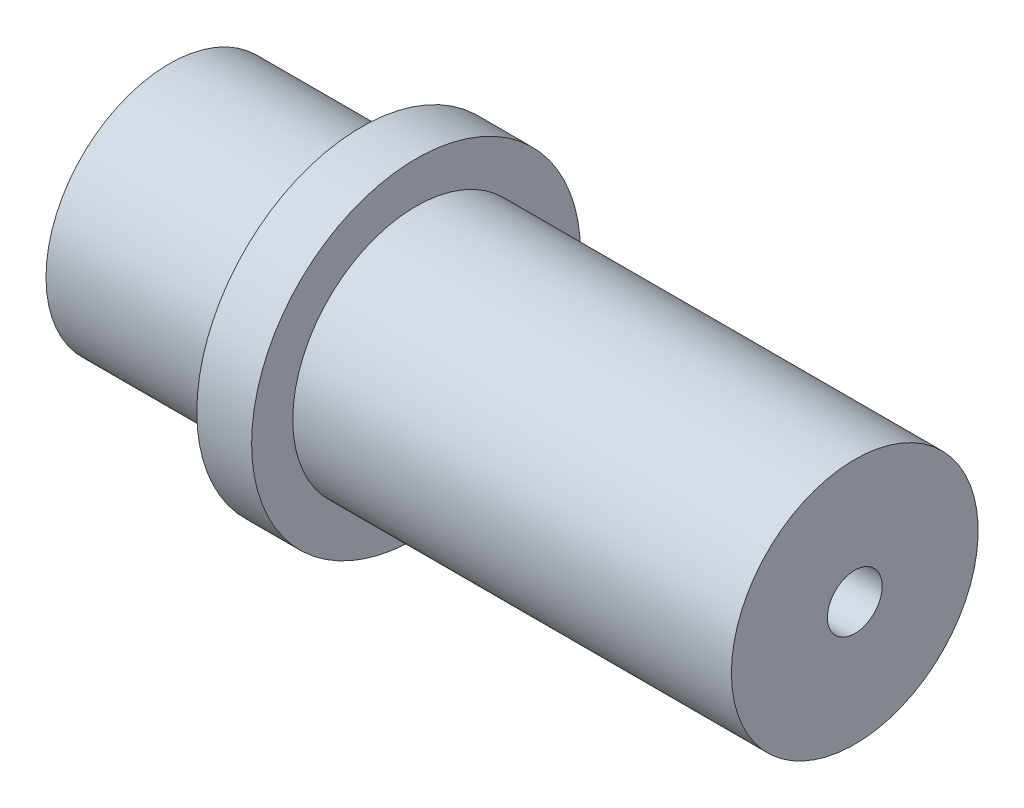
SolidWorks part; units mm, degrees
ref_plane "Front Plane" through (0, 0, 0) normal (0, 0, 1) x (1, 0, 0)
ref_plane "Top Plane" through (0, 0, 0) normal (0, 1, 0) x (1, 0, 0)
ref_plane "Right Plane" through (0, 0, 0) normal (1, 0, 0) x (0, 0, -1)
sketch "Sketch1" plane through (0, 0, 0) normal (0, 0, 1) x (1, 0, 0)
  line L0 (0, 0) -> (95.0095, 0) construction
  line L1 (0, 1.875) -> (0, 5.625)
  line L2 (0, 5.625) -> (8.75, 5.625)
  line L3 (8.75, 5.625) -> (8.75, 7.5)
  line L4 (8.75, 7.5) -> (11.25, 7.5)
  line L5 (11.25, 7.5) -> (11.25, 5.625)
  line L6 (11.25, 5.625) -> (31.25, 5.625)
  line L7 (31.25, 5.625) -> (31.25, 1.25)
  line L8 (31.25, 1.25) -> (21.75, 1.25)
  line L9 (21.75, 1.25) -> (21.75, 1.875)
  line L10 (21.75, 1.875) -> (0, 1.875)
  dimension "D1" = 31.25
  dimension "D2" = 2.5
  dimension "D3" = 20
  dimension "D4" = 21.75
  dimension "D5" = 1.875
  dimension "D6" = 1.25
  dimension "D7" = 5.625
  dimension "D8" = 7.5
revolve "Revolve1" add sketch "Sketch1" angle 360 about L0
